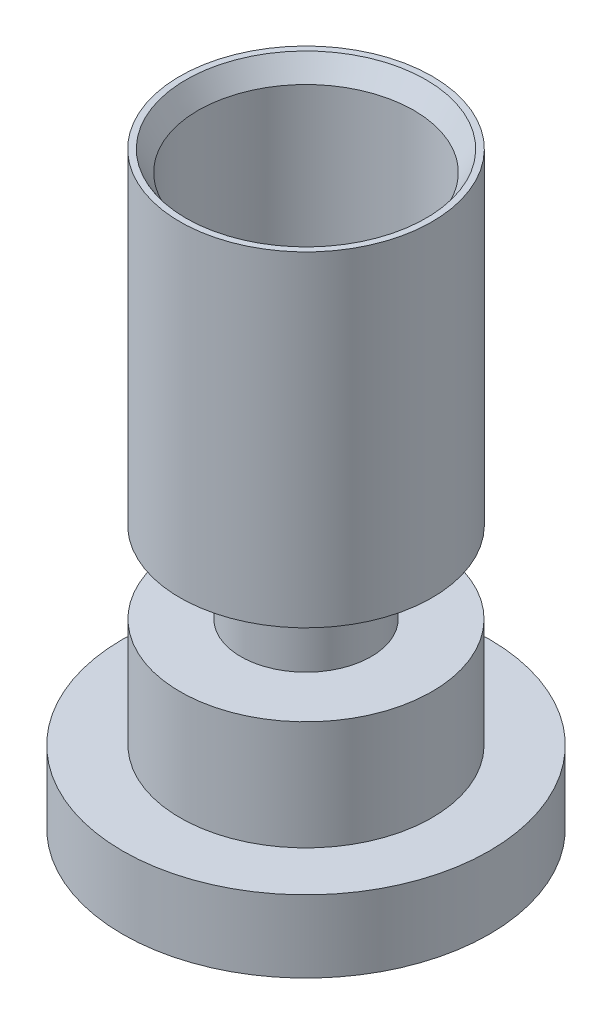
SolidWorks part; units mm, degrees
material "1023 Carbon Steel Sheet (SS)"
ref_plane "Front Plane" through (0, 0, 0) normal (0, 0, 1) x (1, 0, 0)
ref_plane "Top Plane" through (0, 0, 0) normal (0, 1, 0) x (1, 0, 0)
ref_plane "Right Plane" through (0, 0, 0) normal (1, 0, 0) x (0, 0, -1)
sketch "Sketch1" plane through (0, 0, 0) normal (0, 0, 1) x (1, 0, 0)
  line L0 (3.75, 0) -> (3.75, 1.16)
  line L1 (3.75, 1.16) -> (1.6, 1.16)
  line L2 (1.6, 1.16) -> (1.6, 3.45)
  line L3 (1.6, 3.45) -> (0.625, 3.45)
  line L4 (0.625, 3.45) -> (0.625, 6.44)
  line L5 (0.625, 6.44) -> (2.645, 6.44)
  line L6 (2.645, 6.44) -> (2.645, 14.44)
  line L7 (2.645, 14.44) -> (3.095, 14.44)
  line L8 (3.095, 14.44) -> (3.095, 5.95)
  line L9 (3.095, 5.95) -> (1.6, 5.95)
  line L10 (1.6, 5.95) -> (1.6, 4.45)
  line L11 (1.6, 4.45) -> (3.09, 4.45)
  line L12 (3.09, 4.45) -> (3.09, 1.77)
  line L13 (3.09, 1.77) -> (4.5, 1.77)
  line L14 (4.5, 1.77) -> (4.5, 0)
  line L15 (4.5, 0) -> (3.75, 0)
  line L16 (0, 0) -> (0, 14.44) construction
  dimension "D1" = 0.75
  dimension "D2" = 4.5
  dimension "D3" = 1.77
  dimension "D4" = 3.09
  dimension "D5" = 4.45
  dimension "D6" = 1.6
  dimension "D7" = 1.5
  dimension "D8" = 14.44
  dimension "D9" = 0.45
  dimension "D10" = 3.095
  dimension "D11" = 8
  dimension "D12" = 1.16
  dimension "D13" = 3.45
  dimension "D14" = 0.625
revolve "Revolve1" add sketch "Sketch1" angle 360 about L16
chamfer "Chamfer1" distance 0.5 distance2 0.3 1 edges at (0, 14.44, -2.645)
chamfer "Chamfer2" distance 0.5 distance2 0.75 1 edges at (0, 5.95, -3.095)
